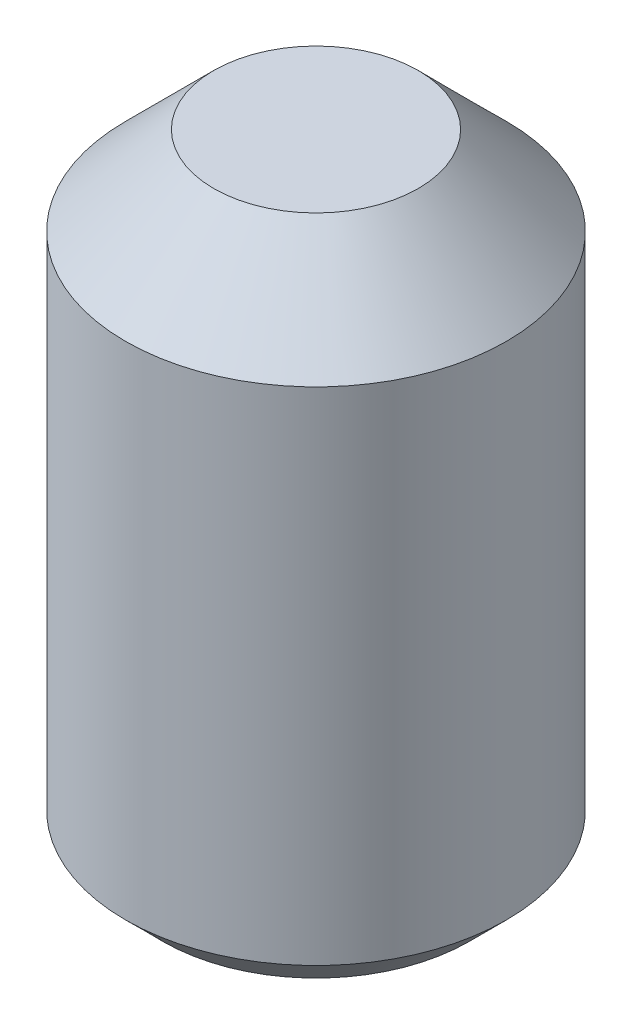
SolidWorks part; units mm, degrees
material "Alloy Steel"
ref_plane "Front Plane" through (0, 0, 0) normal (0, 0, 1) x (1, 0, 0)
ref_plane "Top Plane" through (0, 0, 0) normal (0, 1, 0) x (1, 0, 0)
ref_plane "Right Plane" through (0, 0, 0) normal (1, 0, 0) x (0, 0, -1)
ref_plane "Plane1" through (0, 0, 0) normal (0, 0, -1) x (-1, 0, 0)
sketch "Sketch1" plane through (0, 0, 0) normal (0, 0, -1) x (-1, 0, 0)
  line L0 (-2.413, 0) -> (0, 0)
  line L1 (0, 0) -> (0, 7.9375)
  line L2 (0, 7.9375) -> (-1.2954, 7.9375)
  line L3 (-1.2954, 7.9375) -> (-2.413, 6.8199)
  line L4 (-2.413, 6.8199) -> (-2.413, 0)
  line L5 (0, 0) -> (0, 7.9375) construction
revolve "Revolve1" add sketch "Sketch1" angle 360 about L5
sketch "Sketch2" plane through (0, 0, 0) normal (0, -1, 0) x (1, 0, 0)
  line L0 (-0.687, 1.19) -> (-1.3741, 0)
  line L1 (-1.3741, 0) -> (-0.687, -1.19)
  line L2 (-0.687, -1.19) -> (0.687, -1.19)
  line L3 (0.687, -1.19) -> (1.3741, 0)
  line L4 (1.3741, 0) -> (0.687, 1.19)
  line L5 (0.687, 1.19) -> (-0.687, 1.19)
extrude "Cut-Extrude1" cut sketch "Sketch2" against normal blind 2.54
chamfer "Chamfer1" distance 0.4724 angle 45 1 edges at (-2.413, 0, 0)
